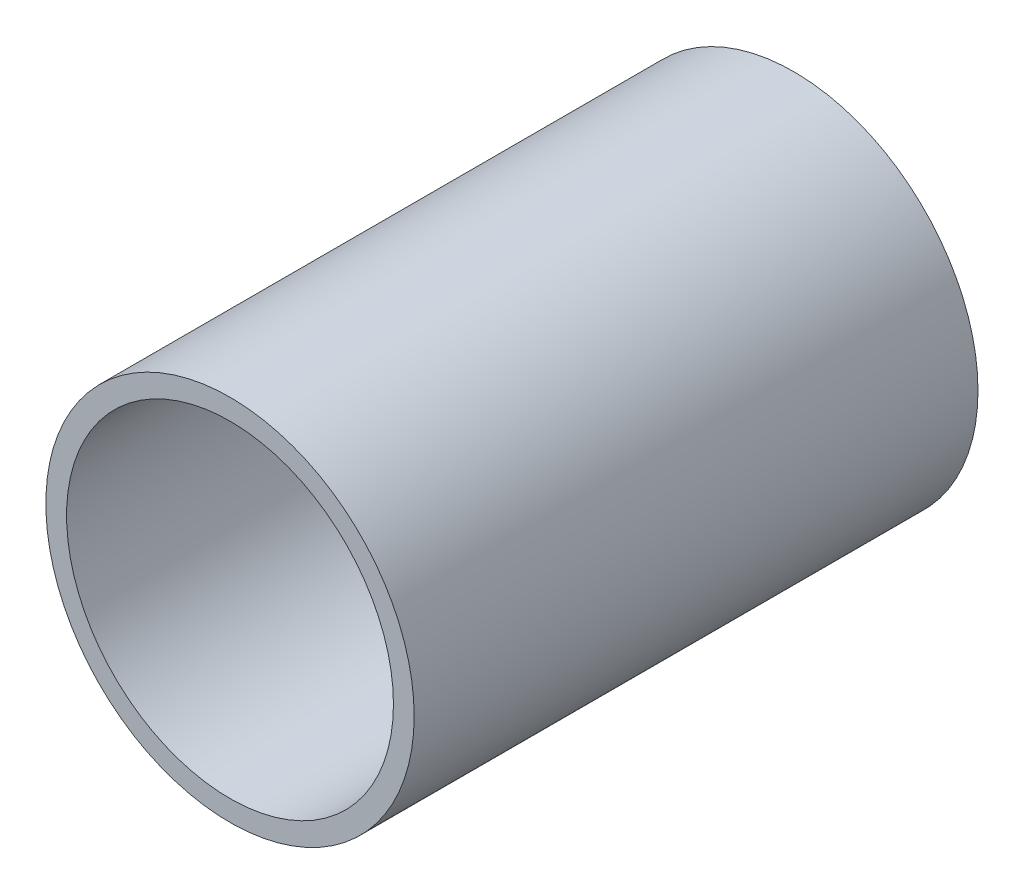
SolidWorks part; units mm, degrees
material "PVC Rigid"
ref_plane "Front Plane" through (0, 0, 0) normal (0, 0, 1) x (1, 0, 0)
ref_plane "Top Plane" through (0, 0, 0) normal (0, 1, 0) x (1, 0, 0)
ref_plane "Right Plane" through (0, 0, 0) normal (1, 0, 0) x (0, 0, -1)
sketch "Sketch1" plane through (0, 0, 0) normal (0, 0, 1) x (1, 0, 0)
  circle A0 centre (0, 0) radius 16.5926
  circle A2 centre (0, 0) radius 14.7257
  dimension "D1" = 33.1851
  dimension "D2" = 1.8669
extrude "Boss-Extrude1" add sketch "Sketch1" along normal blind 50.8
